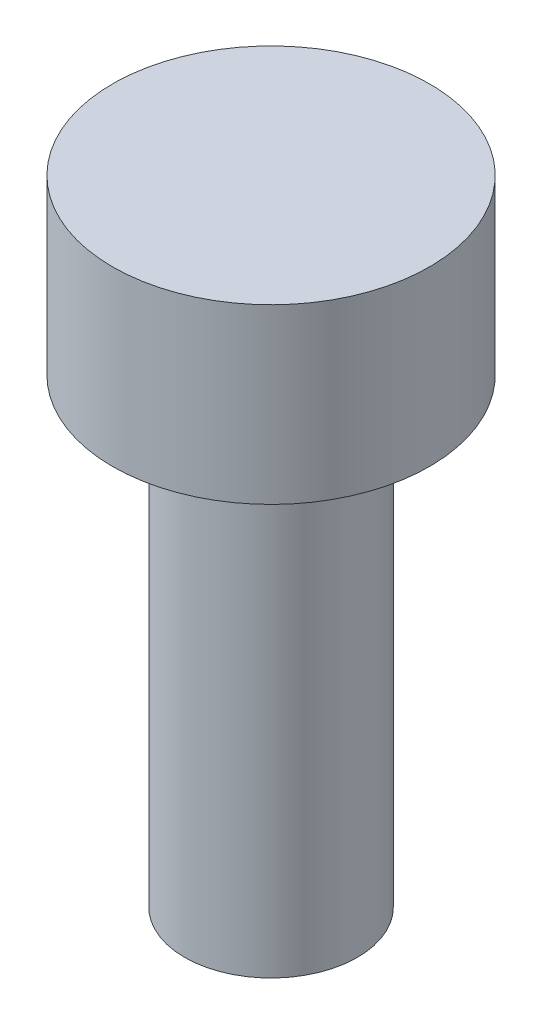
SolidWorks part; units mm, degrees
ref_plane "Front" through (0, 0, 0) normal (0, 0, 1) x (1, 0, 0)
ref_plane "Top" through (0, 0, 0) normal (0, 1, 0) x (1, 0, 0)
ref_plane "Right" through (0, 0, 0) normal (1, 0, 0) x (0, 0, -1)
sketch "profiile" plane through (0, 0, 0) normal (0, 0, 1) x (1, 0, 0)
  line L0 (0, 9.9072) -> (0, -20.7151) construction
  line L1 (0, 3) -> (2.75, 3)
  line L2 (2.75, 3) -> (2.75, 0)
  line L3 (2.75, 0) -> (1.5, 0)
  line L4 (1.5, 0) -> (1.5, -8)
  line L5 (1.5, -8) -> (0, -8)
  line L6 (0, -8) -> (0, 3)
  dimension "D1" = 5.5
  dimension "D2" = 3
  dimension "thread_length" = 8
  dimension "D4" = 3
revolve "Base-Revolve" add sketch "profiile" angle 360 about L0
